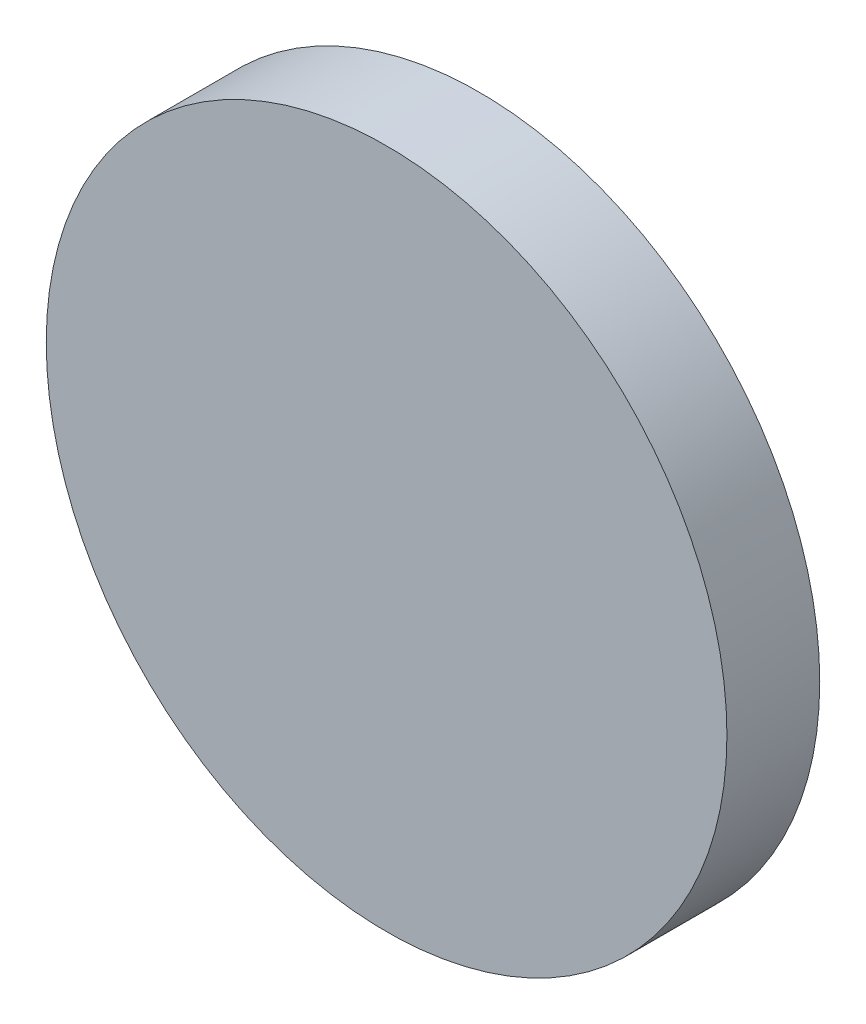
SolidWorks part; units mm, degrees
material "Латунь"
ref_plane "Спереди" through (0, 0, 0) normal (0, 0, 1) x (1, 0, 0)
ref_plane "Сверху" through (0, 0, 0) normal (0, 1, 0) x (1, 0, 0)
ref_plane "Справа" through (0, 0, 0) normal (1, 0, 0) x (0, 0, -1)
sketch "Эскиз1" plane through (0, 0, 0) normal (0, 0, 1) x (1, 0, 0)
  circle A0 centre (0, 0) radius 11
  dimension "D1" = 22
extrude "Бобышка-Вытянуть4" add sketch "Эскиз1" along normal blind 3
